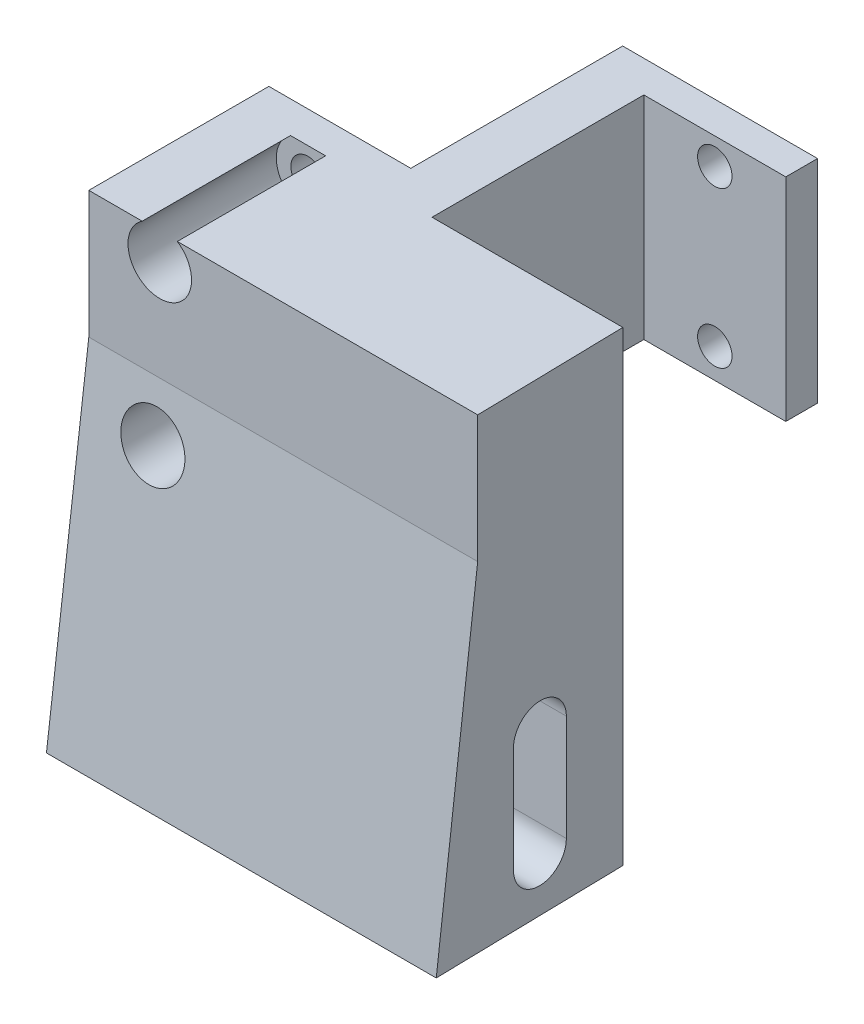
SolidWorks part; units mm, degrees
ref_plane "Front Plane" through (0, 0, 0) normal (0, 0, 1) x (1, 0, 0)
ref_plane "Top Plane" through (0, 0, 0) normal (0, 1, 0) x (1, 0, 0)
ref_plane "Right Plane" through (0, 0, 0) normal (1, 0, 0) x (0, 0, -1)
sketch "Sketch1" plane through (0, 0, 0) normal (0, 1, 0) x (1, 0, 0)
  line L0 (0, 0) -> (18.4, 0)
  line L1 (18.4, 0) -> (18.4, 20)
  line L2 (18.4, 20) -> (31.8, 20)
  line L3 (31.8, 20) -> (31.8, 23)
  line L4 (31.8, 23) -> (13.4, 23)
  line L5 (13.4, 23) -> (13.4, 3)
  line L6 (13.4, 3) -> (0, 3)
  line L7 (0, 3) -> (0, 0)
  dimension "D1" = 13.4
  dimension "D2" = 5
  dimension "D3" = 3
  dimension "D4" = 17
extrude "Boss-Extrude1" add sketch "Sketch1" along normal blind 20
sketch "Sketch2" plane through (0, 0, -20) normal (0, 0, 1) x (1, 0, 0)
  line L0 (25.1, 20) -> (25.1, 0) construction
  line L3 (18.4, 20) -> (31.8, 20) construction
  line L4 (18.4, 0) -> (31.8, 0) construction
  circle A0 centre (25.1, 2.8) radius 1.625
  circle A1 centre (25.1, 17.5) radius 1.625
  point P10 (24.9499, 17.0747)
  point P11 (25.1, 17.1465)
  point P12 (25.1, 4.9124)
  dimension "D1" = 3.25
  dimension "D2" = 2.5
  dimension "D3" = 14.7
extrude "Cut-Extrude1" cut sketch "Sketch2" against normal through all both and the other way through all
ref_plane "Plane1" through (15.9, 0, 0) normal (-1, 0, 0) x (0, 0, 1)
mirror "Mirror1" about plane through (15.9, 0, 0) normal (-1, 0, 0) of "Cut-Extrude1"
sketch "Sketch3" plane through (0, 0, 0) normal (-1, 0, 0) x (0, 0, 1)
  line L0 (0, 0) -> (0, -24)
  line L1 (0, -24) -> (18, -24)
  line L2 (18, -24) -> (14, 8)
  line L3 (14, 8) -> (14, 20)
  line L4 (14, 20) -> (0, 20)
  line L5 (0, 20) -> (0, 0) construction
  line L6 (0, 20) -> (0, 0)
  line L7 (8, -9) -> (8, -19) construction
  line L8 (10.55, -9) -> (10.55, -19)
  line L9 (5.45, -9) -> (5.45, -19)
  arc A0 (10.55, -9) -> (5.45, -9) centre (8, -9) ccw
  arc A1 (5.45, -19) -> (10.55, -19) centre (8, -19) ccw
  point P3 (8, -14)
  dimension "D1" = 18
  dimension "D2" = 14
  dimension "D3" = 12
  dimension "D4" = 44
  dimension "D5" = 10
  dimension "D6" = 5.1
  dimension "D7" = 8
  dimension "D8" = 5
extrude "Boss-Extrude2" add sketch "Sketch3" against normal offset from surface (36.8 mm away) 5 up to face at (31.8, 10, -21.5) offset beyond the face yes
sketch "Sketch4" plane through (0, -24, 0) normal (0, -1, 0) x (1, 0, 0)
  line L4 (36.8, 18) -> (36.4167, 0)
  line L5 (36.8, 0) -> (0, 0) construction
  line L6 (36.4167, 0) -> (36.8, 0)
  line L7 (36.8, 0) -> (36.8, 18)
  dimension "D1" = 1.22
extrude "Cut-Extrude2" cut sketch "Sketch4" against normal through all
sketch "Sketch5" plane through (0, 0, 0) normal (-1, 0, 0) x (0, 0, 1)
  line L0 (14, -9) -> (14, -24)
  line L1 (0, -24) -> (18, -24) construction
  line L2 (14, -24) -> (2, -24)
  line L3 (2, -24) -> (2, -9)
  arc A0 (14, -9) -> (2, -9) centre (8, -9) ccw
  arc A1 (10.55, -9) -> (5.45, -9) centre (8, -9) ccw construction
  dimension "D1" = 12
extrude "Cut-Extrude3" cut sketch "Sketch5" against normal offset from surface (31.7137 mm away) 5
sketch "Sketch6" plane through (0, 0, 0) normal (0, 0, -1) x (-1, 0, 0)
  circle A0 centre (-6.7, 2.8) radius 3
  circle A1 centre (-6.7, 17.5) radius 3
  dimension "D1" = 6
extrude "Cut-Extrude4" cut sketch "Sketch6" against normal through all
